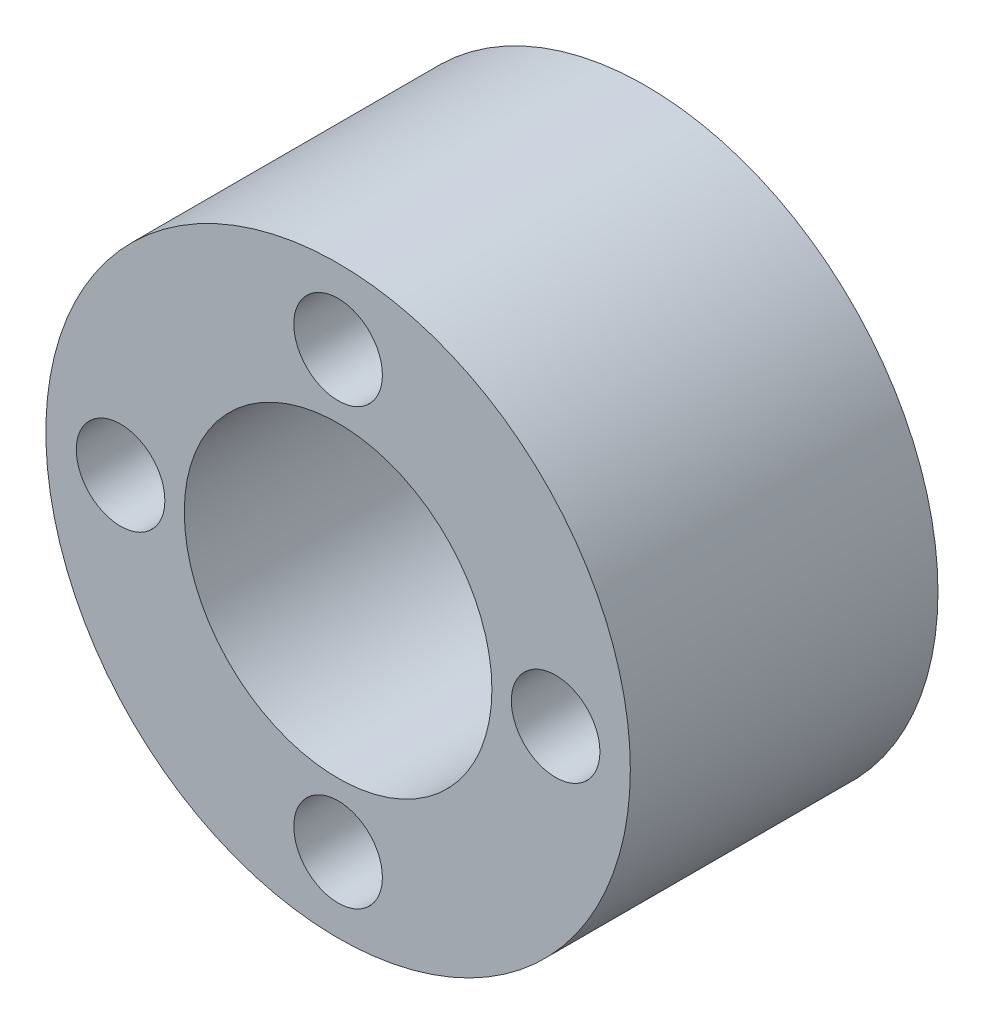
SolidWorks part; units mm, degrees
ref_plane "Front Plane" through (0, 0, 0) normal (0, 0, 1) x (1, 0, 0)
ref_plane "Top Plane" through (0, 0, 0) normal (0, 1, 0) x (1, 0, 0)
ref_plane "Right Plane" through (0, 0, 0) normal (1, 0, 0) x (0, 0, -1)
sketch "Sketch1" plane through (0, 0, 0) normal (0, 0, 1) x (1, 0, 0)
  line L1 (-8.9803, 0) -> (0, -8.9803) construction
  line L2 (0, -8.9803) -> (8.9803, 0) construction
  line L3 (8.9803, 0) -> (0, 8.9803) construction
  line L4 (0, 8.9803) -> (-8.9803, 0) construction
  circle A0 centre (0, 0) radius 6.35
  circle A1 centre (0, 0) radius 12.065
  circle A3 centre (-8.9803, 0) radius 1.8288
  circle A4 centre (8.9803, 0) radius 1.8288
  circle A6 centre (0, 8.9803) radius 1.8288
  circle A7 centre (0, -8.9803) radius 1.8288
  dimension "D1" = 12.7
  dimension "D2" = 24.13
  dimension "D3" = 3.6576
  dimension "D4" = 12.7
extrude "Boss-Extrude1" add sketch "Sketch1" along normal blind 12.7
